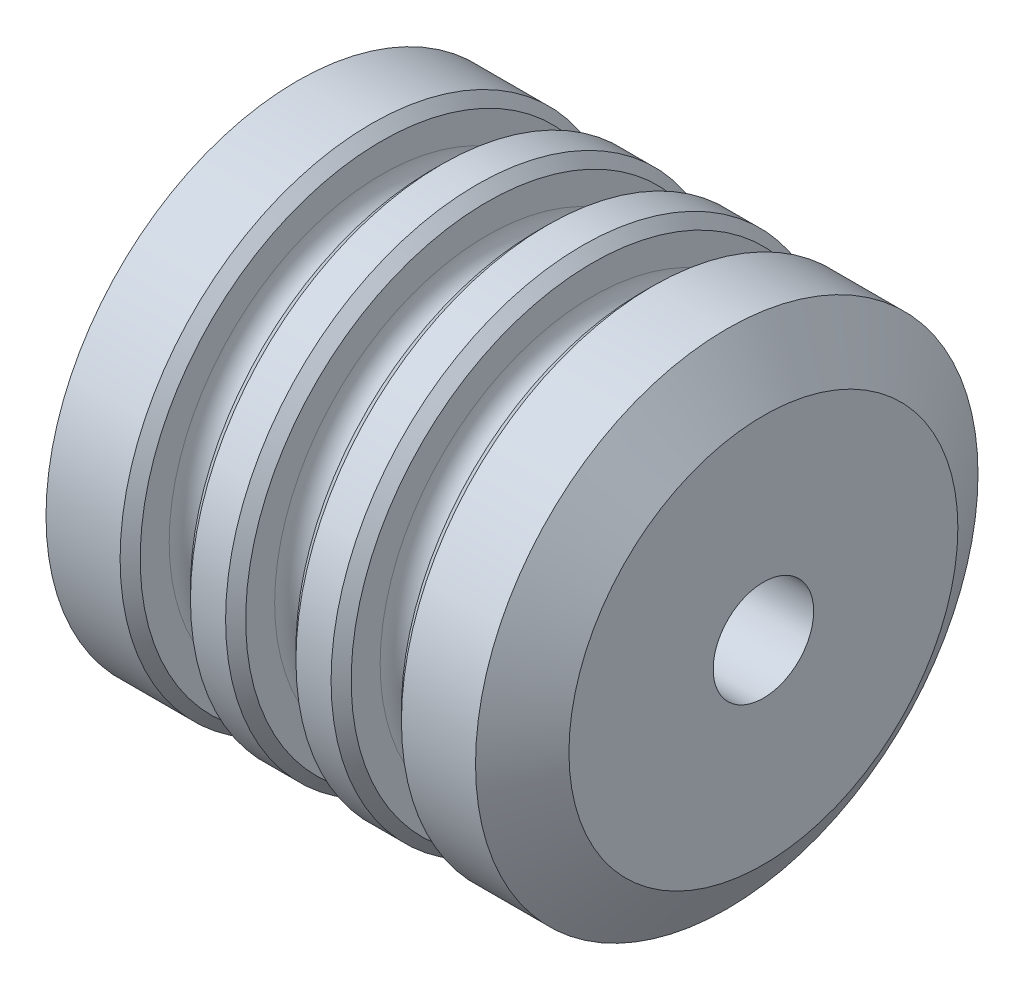
SolidWorks part; units mm, degrees
ref_plane "Front Plane" through (0, 0, 0) normal (0, 0, 1) x (1, 0, 0)
ref_plane "Top Plane" through (0, 0, 0) normal (0, 1, 0) x (1, 0, 0)
ref_plane "Right Plane" through (0, 0, 0) normal (1, 0, 0) x (0, 0, -1)
sketch "Sketch2" plane through (0, 0, 0) normal (0, 0, 1) x (1, 0, 0)
  line L0 (0, 0) -> (-500.3265, 0) construction
  line L1 (0, 0) -> (0, 193.5078)
  line L2 (-36.4614, 250) -> (-110.1958, 250)
  line L3 (-120.1958, 240) -> (-120.1958, 211.1622)
  line L4 (-144.1958, 187.1622) -> (-146.1958, 187.1622)
  line L5 (-170.1958, 211.1622) -> (-170.1958, 240)
  line L6 (-180.1958, 250) -> (-215.1633, 250)
  line L7 (-225.1633, 240) -> (-225.1633, 211.1622)
  line L8 (-249.1633, 187.1622) -> (-251.1633, 187.1622)
  line L9 (-275.1633, 211.1622) -> (-275.1633, 240)
  line L10 (-285.1633, 250) -> (-320.1307, 250)
  line L11 (-330.1307, 240) -> (-330.1307, 211.1622)
  line L12 (-354.1307, 187.1622) -> (-356.1307, 187.1622)
  line L13 (-380.1307, 211.1622) -> (-380.1307, 240)
  line L14 (-390.1307, 250) -> (-463.8651, 250)
  line L15 (-500.3265, 193.5078) -> (-500.3265, 0)
  line L16 (-380.1307, 240) -> (-390.1307, 250)
  line L17 (-390.1307, 250) -> (-320.1307, 250) construction
  line L18 (-330.1307, 240) -> (-320.1307, 250)
  line L19 (-500.3265, 187.1622) -> (0, 187.1622) construction
  line L21 (-250.1633, 0) -> (-250.1633, 250) construction
  line L22 (-500.3265, 193.5078) -> (-463.8651, 250)
  line L23 (0, 193.5078) -> (-36.4614, 250)
  line L24 (-500.3265, 250) -> (-500.3265, 193.5078) construction
  line L25 (-463.8651, 250) -> (-500.3265, 250) construction
  line L26 (0, 250) -> (-36.4614, 250) construction
  line L27 (0, 193.5078) -> (0, 250) construction
  line L28 (0, 0) -> (-500.3265, 0)
  line L29 (-275.1633, 240) -> (-285.1633, 250)
  line L30 (-225.1633, 240) -> (-215.1633, 250)
  line L31 (-180.1958, 250) -> (-170.1958, 240)
  line L32 (-120.1958, 240) -> (-110.1958, 250)
  line L33 (-285.1633, 250) -> (-215.1633, 250) construction
  line L34 (-180.1958, 250) -> (-110.1958, 250) construction
  line L35 (-120.1958, 240) -> (-170.1958, 240) construction
  line L36 (-225.1633, 240) -> (-275.1633, 240) construction
  line L38 (-380.1307, 240) -> (-330.1307, 240) construction
  arc A0 (-120.1958, 211.1622) -> (-144.1958, 187.1622) centre (-144.1958, 211.1622) cw
  arc A1 (-146.1958, 187.1622) -> (-170.1958, 211.1622) centre (-146.1958, 211.1622) cw
  arc A2 (-225.1633, 211.1622) -> (-249.1633, 187.1622) centre (-249.1633, 211.1622) cw
  arc A3 (-251.1633, 187.1622) -> (-275.1633, 211.1622) centre (-251.1633, 211.1622) cw
  arc A4 (-330.1307, 211.1622) -> (-354.1307, 187.1622) centre (-354.1307, 211.1622) cw
  arc A5 (-356.1307, 187.1622) -> (-380.1307, 211.1622) centre (-356.1307, 211.1622) cw
  point P5 (-463.8651, 250)
  dimension "D3" = 24
  dimension "D1" = 250
  dimension "D2" = 50
revolve "Revolve1" add sketch "Sketch2" angle 360 about L28
sketch "Sketch3" plane through (0, 0, 0) normal (1, 0, 0) x (0, 0, -1)
  circle A0 centre (0, 0) radius 50
extrude "Cut-Extrude1" cut sketch "Sketch3" against normal blind 550
